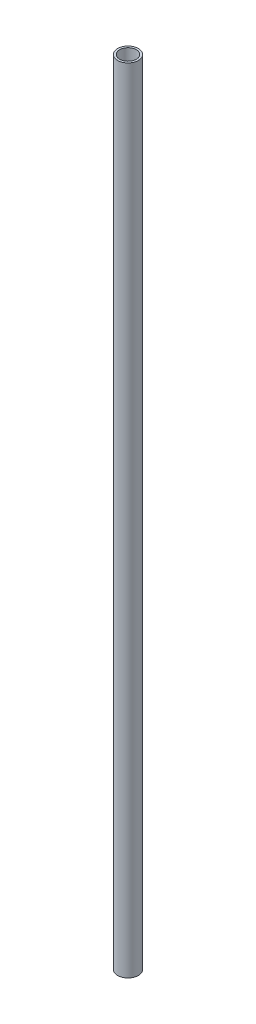
SolidWorks part; units mm, degrees
material "Thornel Mat VMA"
ref_plane "前视基准面" through (0, 0, 0) normal (0, 0, 1) x (1, 0, 0)
ref_plane "上视基准面" through (0, 0, 0) normal (0, 1, 0) x (1, 0, 0)
ref_plane "右视基准面" through (0, 0, 0) normal (1, 0, 0) x (0, 0, -1)
sketch "草图1" plane through (0, 0, 0) normal (0, 1, 0) x (1, 0, 0)
  circle A0 centre (0, 0) radius 10
  circle A1 centre (0, 0) radius 8
extrude "凸台-拉伸1" add sketch "草图1" along normal blind 763
